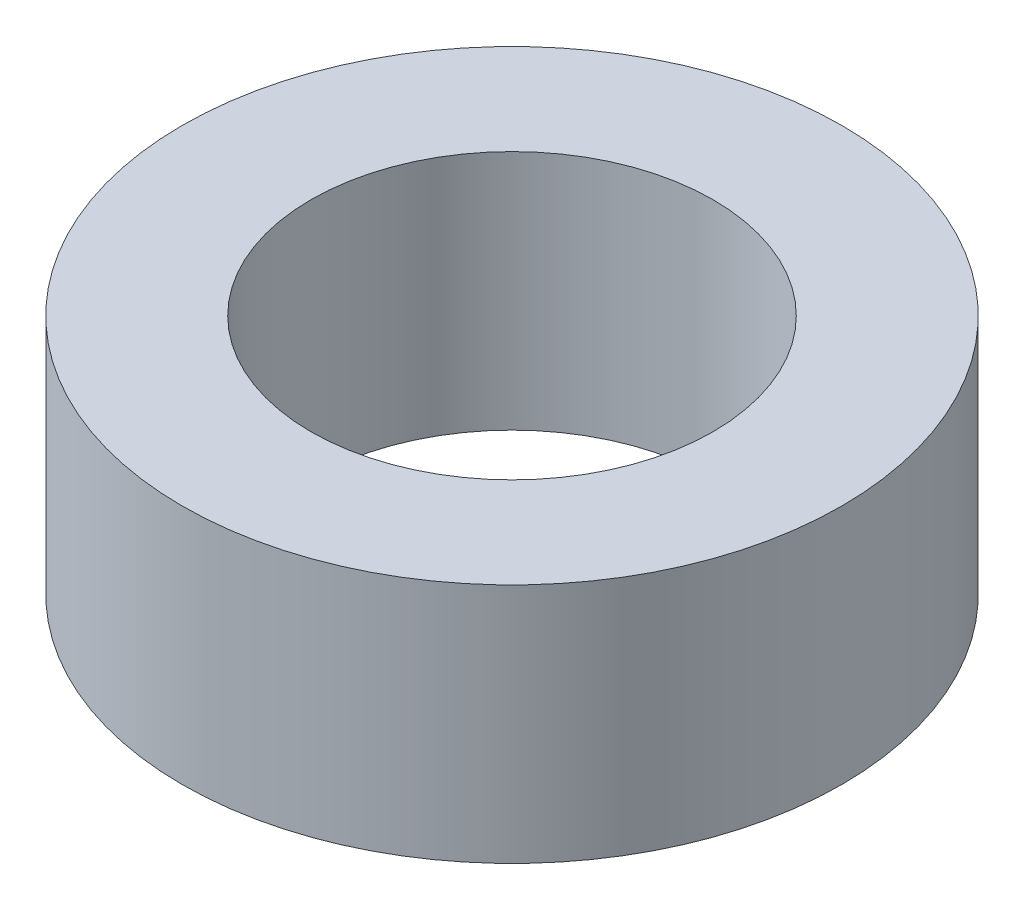
SolidWorks part; units mm, degrees
ref_plane "Alzado" through (0, 0, 0) normal (0, 0, 1) x (1, 0, 0)
ref_plane "Planta" through (0, 0, 0) normal (0, 1, 0) x (1, 0, 0)
ref_plane "Vista lateral" through (0, 0, 0) normal (1, 0, 0) x (0, 0, -1)
sketch "Croquis1" plane through (0, 0, 0) normal (0, 1, 0) x (1, 0, 0)
  circle A0 centre (0, 0) radius 12.5
  circle A1 centre (0, 0) radius 20.5
  dimension "D1" = 8
  dimension "D2" = 25
extrude "Saliente-Extruir1" add sketch "Croquis1" along normal blind 15
